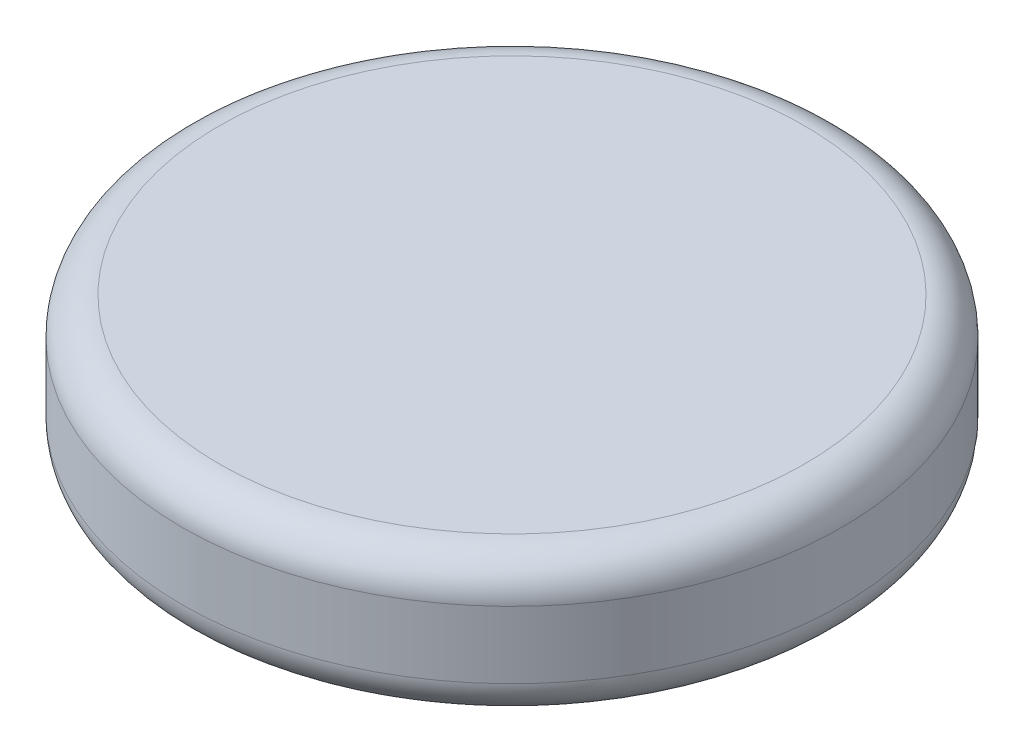
SolidWorks part; units mm, degrees
ref_plane "Front Plane" through (0, 0, 0) normal (0, 0, 1) x (1, 0, 0)
ref_plane "Top Plane" through (0, 0, 0) normal (0, 1, 0) x (1, 0, 0)
ref_plane "Right Plane" through (0, 0, 0) normal (1, 0, 0) x (0, 0, -1)
sketch "Sketch1" plane through (0, 0, 0) normal (0, 1, 0) x (1, 0, 0)
  circle A0 centre (0, 0) radius 15.9385
  dimension "D1" = 31.877
extrude "Boss-Extrude1" add sketch "Sketch1" along normal blind 6.7945 contours A0
fillet "Fillet1" radius 1.778 2 edges at (0, 0, 15.9385) (0, 6.7945, 15.9385)
